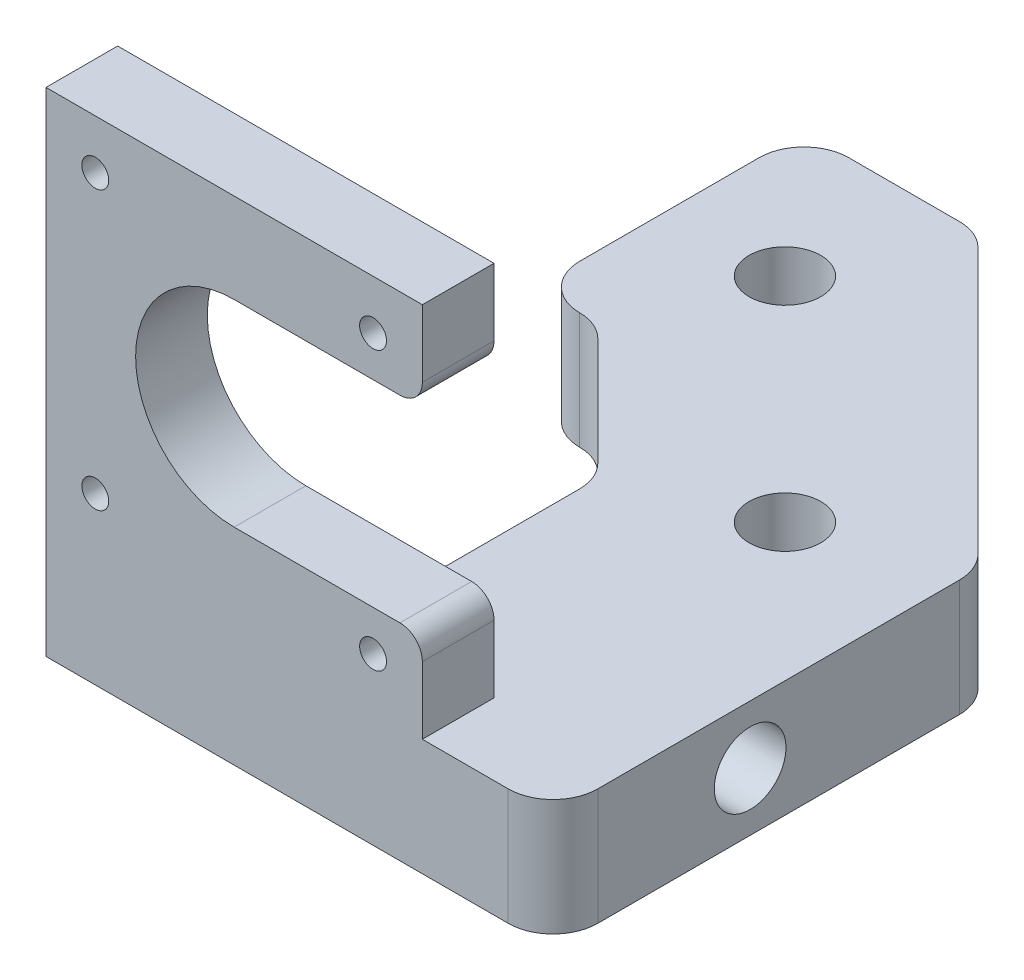
SolidWorks part; units mm, degrees
ref_plane "Front Plane" through (0, 0, 0) normal (0, 0, 1) x (1, 0, 0)
ref_plane "Top Plane" through (0, 0, 0) normal (0, 1, 0) x (1, 0, 0)
ref_plane "Right Plane" through (0, 0, 0) normal (1, 0, 0) x (0, 0, -1)
sketch "Sketch1" plane through (0, 0, 0) normal (0, 1, 0) x (1, 0, 0)
  line L0 (-26.25, -50) -> (30.3312, -50)
  line L1 (0.3312, -15) -> (-14.6688, 0)
  line L2 (30.3312, -2.5736) -> (30.3312, -50)
  line L3 (-2.2424, 30) -> (30.3312, -2.5736)
  line L4 (-21.6688, 0) -> (-21.6688, 30)
  line L6 (-14.6688, 0) -> (-21.6688, 0)
  line L7 (0.3312, -42) -> (0.3312, -15)
  line L8 (-21.6688, 30) -> (-2.2424, 30)
  line L11 (-26.25, -50) -> (-26.25, -42)
  line L13 (-26.25, -42) -> (0.3312, -42)
  circle A0 centre (-8.7868, 15) radius 4
  circle A1 centre (15, -8.7868) radius 4
extrude "Extrude1" add sketch "Sketch1" along normal blind 13
fillet "Fillet5" radius 5 5 edges at (-2.2424, 6.5, -30) (-14.6688, 6.5, 0) (0.3312, 6.5, 15) (30.3312, 6.5, 50) (30.3312, 6.5, 2.5736)
fillet "Fillet6" radius 5 2 edges at (-21.6688, 6.5, 0) (-21.6688, 6.5, -30)
sketch "Sketch8" plane through (0.3312, 0, 0) normal (-1, 0, 0) x (0, 0, 1)
  circle A0 centre (28, 6.5) radius 4
extrude "Extrude7" cut sketch "Sketch8" against normal blind 30
sketch "Sketch9" plane through (0, 13, 0) normal (0, 1, 0) x (-1, 0, 0)
  line L0 (26.25, 50) -> (-25.3312, 50) construction
  line L1 (26.25, 42) -> (-15.75, 42)
  line L2 (26.25, 42) -> (26.25, 50)
  line L3 (26.25, 50) -> (-15.75, 50)
  line L4 (-15.75, 42) -> (-15.75, 50)
extrude "Extrude8" add sketch "Sketch9" along normal blind 42
sketch "Sketch10" plane through (0, 0, 50) normal (0, 0, 1) x (1, 0, 0)
  circle A0 centre (-5.25, 34) radius 11
  circle A1 centre (10.25, 49.5) radius 1.5
  circle A2 centre (-20.75, 49.5) radius 1.5
  circle A3 centre (-20.75, 18.5) radius 1.5
  circle A4 centre (10.25, 18.5) radius 1.5
extrude "Extrude9" cut sketch "Sketch10" against normal up to next
sketch "Sketch11" plane through (0, 0, 42) normal (0, 0, -1) x (-1, 0, 0)
  line L0 (5.25, 45) -> (-15.75, 45)
  line L1 (-15.75, 55) -> (-15.75, 13) construction
  line L2 (5.25, 23) -> (-15.75, 23)
  line L3 (-15.75, 23) -> (-15.75, 45)
  line L4 (5.25, 45) -> (5.25, 23)
  circle A0 centre (5.25, 34) radius 11 construction
extrude "Extrude10" cut sketch "Sketch11" against normal up to next
fillet "Fillet7" radius 2.5 2 edges at (15.75, 23, 46) (15.75, 45, 46)
